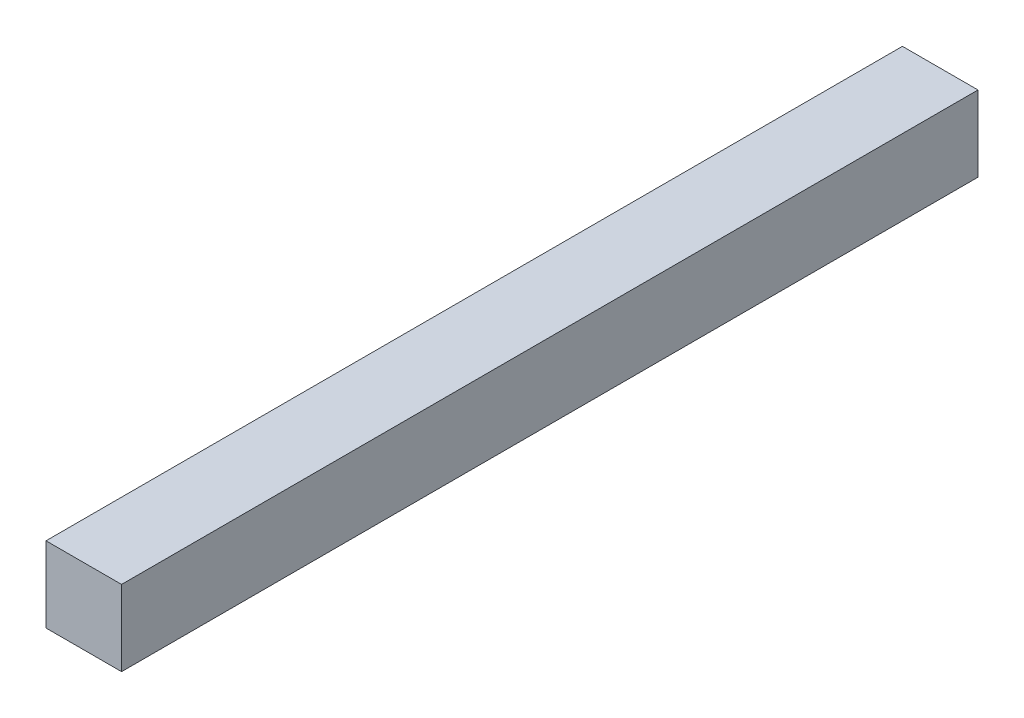
SolidWorks part; units mm, degrees
ref_plane "Plan de face" through (0, 0, 0) normal (0, 0, 1) x (1, 0, 0)
ref_plane "Plan de dessus" through (0, 0, 0) normal (0, 1, 0) x (1, 0, 0)
ref_plane "Plan de droite" through (0, 0, 0) normal (1, 0, 0) x (0, 0, -1)
sketch "Esquisse1" plane through (0, 0, 0) normal (0, 0, 1) x (1, 0, 0)
  line L1 (-7.5, -7.5) -> (7.5, -7.5)
  line L2 (-7.5, -7.5) -> (-7.5, 7.5)
  line L3 (-7.5, 7.5) -> (7.5, 7.5)
  line L4 (7.5, -7.5) -> (7.5, 7.5)
  line L5 (-7.5, -7.5) -> (7.5, 7.5) construction
  line L6 (-7.5, 7.5) -> (7.5, -7.5) construction
  point P0 (0, 0)
  dimension "D1" = 15
  dimension "D2" = 15
extrude "Boss.-Extru.1" add sketch "Esquisse1" along normal blind 170
